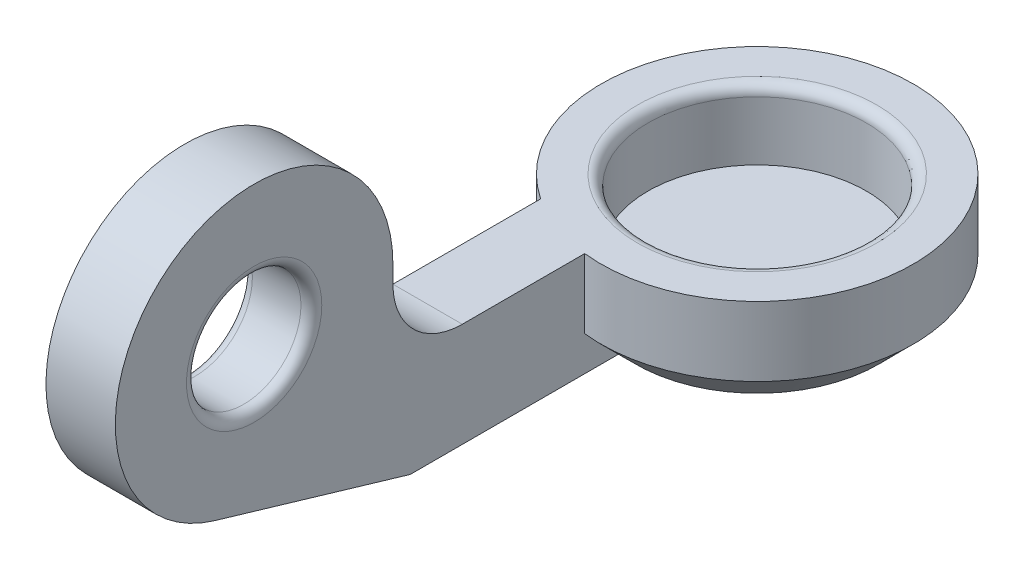
SolidWorks part; units mm, degrees
ref_plane "前视基准面" through (0, 0, 0) normal (0, 0, 1) x (1, 0, 0)
ref_plane "上视基准面" through (0, 0, 0) normal (0, 1, 0) x (1, 0, 0)
ref_plane "右视基准面" through (0, 0, 0) normal (1, 0, 0) x (0, 0, -1)
ref_plane "基准面4" through (0, 0, 5) normal (0, 0, 1) x (1, 0, 0)
sketch "草图6" plane through (0, 0, 0) normal (0, 1, 0) x (1, 0, 0)
  circle A1 centre (0, 0) radius 4.5
  dimension "D2" = 9
extrude "凸台-拉伸4" add sketch "草图6" against normal blind 3
sketch "草图7" plane through (0, 0, 0) normal (0, 1, 0) x (1, 0, 0)
  circle A0 centre (0, 0) radius 3.15
  dimension "D1" = 6.3
extrude "切除-拉伸4" cut sketch "草图7" against normal blind 2
sketch "草图15" plane through (0, 0, 0) normal (1, 0, 0) x (0, 0, -1)
  line L0 (4.5, -3) -> (4.5, -2)
  line L1 (4.5, -3) -> (4.5, 0) construction
  line L2 (4.5, -2) -> (3.5, -3)
  line L3 (-4.5, -3) -> (4.5, -3) construction
  line L4 (3.5, -3) -> (4.5, -3)
  line L5 (0, 0) -> (0, -5.1647) construction
  dimension "D1" = 1
  dimension "D2" = 1
revolve "切除-旋转2" cut sketch "草图15" angle 360 about L5
ref_plane "基准面11" through (-0.5, 0, 0) normal (1, 0, 0) x (0, 0, -1)
sketch "草图8" plane through (-0.5, 0, 0) normal (1, 0, 0) x (0, 0, -1)
  line L0 (0, -3) -> (0, 6.4628) construction
  line L1 (-4.5, -3) -> (4.5, -3) construction
  line L2 (4.5, 0) -> (-4.5, 0) construction
  circle A0 centre (-14, 2.5) radius 4
  dimension "D2" = 8
  dimension "D1" = 14
  dimension "D3" = 2.5
extrude "凸台-拉伸5" add sketch "草图8" against normal blind 2 separate body
sketch "草图9" plane through (-0.5, 0, 0) normal (1, 0, 0) x (0, 0, -1)
  line L1 (4.5, 0) -> (-4.5, 0) construction
  line L2 (-9.5, -3) -> (-15.1331, -1.3362)
  line L3 (-14, 2.5) -> (-15.1331, -1.3362) construction
  line L4 (-14, 2.5) -> (-6.3447, 2.0026) construction
  line L10 (-4.5, -3) -> (4.5, -3) construction
  line L11 (-3.529, -3) -> (-9.5, -3)
  line L12 (-6.3447, 2.0026) -> (-3.5, 0)
  line L13 (-3.5, 0) -> (-3.5, -3)
  line L14 (-3.5, -3) -> (-3.529, -3)
  line L15 (-4.5, 0) -> (-12.5276, 0) construction
  line L16 (-14, 2.5) -> (-3.0944, 2.5) construction
  line L17 (-15.1331, -1.3362) -> (-10.7493, 0.1692)
  line L18 (-10.7493, 0.1692) -> (-10, 2.5)
  line L19 (-10, 2.5) -> (-6.3447, 2.0026)
  circle A0 centre (-14, 2.5) radius 4 construction
  dimension "D1" = 3.5
extrude "凸台-拉伸7" add sketch "草图9" against normal up to surface (2 mm away) up to face at (-2.5, 2.5, 10)
sketch "草图16" plane through (0, 0, 3.5) normal (0, 0, -1) x (-1, 0, 0)
  line L0 (2.5, -3) -> (2.5, -2.1988)
  line L1 (2.5, -2.1988) -> (0.5, -2.9557)
  line L2 (0.5, -2.9557) -> (0.5, -3)
  line L3 (0.5, -3) -> (2.5, -3)
extrude "凸台-拉伸8" add sketch "草图16" along normal up to next
sketch "草图11" plane through (-0.5, 0, 0) normal (1, 0, 0) x (0, 0, -1)
  circle A0 centre (-14, 2.5) radius 1.65
  dimension "D1" = 3.3
extrude "切除-拉伸6" cut sketch "草图11" against normal blind 2
sketch "草图12" plane through (-2.5, 0, 0) normal (-1, 0, 0) x (0, 0, 1)
  line L0 (3.5, 0) -> (3.7417, 0)
  line L2 (6.3447, 2.0026) -> (3.5, 0)
  line L5 (6.3447, 2.0026) -> (10, 2.5)
  line L6 (3.7417, 0) -> (10, 0)
  line L7 (10, 0) -> (10, 2.5)
extrude "切除-拉伸7" cut sketch "草图12" against normal up to next
fillet "圆角4" radius 2 1 edges at (-1.5, 0, 10)
fillet "圆角1" radius 0.3 1 edges at (0, 0, 3.15)
fillet "圆角2" radius 0.3 1 edges at (-0.5, 2.5, 12.35)
ref_plane "基准面13" through (0, 0, 9) normal (0, 0, 1) x (1, 0, 0)
sketch "草图14" plane through (0, 0, 9) normal (0, 0, 1) x (1, 0, 0)
  line L0 (-6.6956, 2.5) -> (6.2787, 2.5) construction
  line L1 (-0.5, 6.5) -> (-2.5, 6.5) construction
  line L2 (-2.8, 2.5) -> (-2.5, 2.5)
  line L4 (-2.5, 2.5) -> (-2.5, 6.5)
  arc A0 (-2.5, 6.5) -> (-2.8, 2.5) centre (34.8421, 1.6881) ccw
  dimension "D1" = 4
  dimension "D2" = 0.3
revolve "旋转3" [suppressed] add sketch "草图14" angle 360 about L0
fillet "圆角3" radius 0.3 1 edges at (-2.5, 2.5, 12.35)
